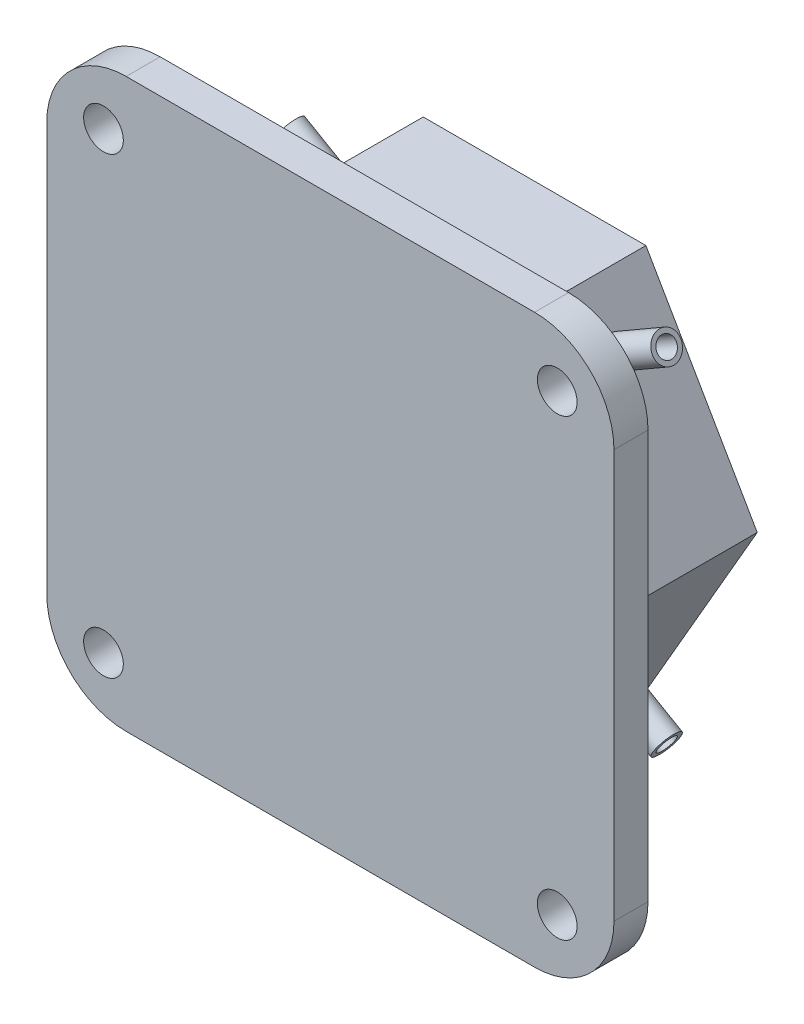
SolidWorks part; units mm, degrees
ref_plane "前视基准面" through (0, 0, 0) normal (0, 0, 1) x (1, 0, 0)
ref_plane "上视基准面" through (0, 0, 0) normal (0, 1, 0) x (1, 0, 0)
ref_plane "右视基准面" through (0, 0, 0) normal (1, 0, 0) x (0, 0, -1)
other "Configuration Table"
sketch "草图1" plane through (0, 0, 0) normal (0, 0, 1) x (1, 0, 0)
  line L1 (-18, -25) -> (18, -25)
  line L2 (-25, -18) -> (-25, 18)
  line L3 (-18, 25) -> (18, 25)
  line L4 (25, -18) -> (25, 18)
  line L5 (-25, -25) -> (25, 25) construction
  line L6 (-25, 25) -> (25, -25) construction
  circle A0 centre (20, 20) radius 1.75
  circle A1 centre (-20, 20) radius 1.75
  circle A2 centre (-20, -20) radius 1.75
  circle A3 centre (20, -20) radius 1.75
  arc A4 (18, -25) -> (25, -18) centre (18, -18) ccw
  arc A5 (-18, -25) -> (-25, -18) centre (-18, -18) cw
  arc A6 (18, 25) -> (25, 18) centre (18, 18) cw
  arc A7 (-25, 18) -> (-18, 25) centre (-18, 18) cw
  point P0 (0, 0)
  point P6 (20, 20)
  dimension "D3" = 5
  dimension "D6" = 3.5
  dimension "D7" = 3.5
  dimension "D4" = 3.5
  dimension "D8" = 3.5
  dimension "D11" = 7
  dimension "D1" = 50
  dimension "D2" = 50
  dimension "D5" = 5
  dimension "D9" = 5
  dimension "D10" = 5
extrude "凸台-拉伸3" add sketch "草图1" along normal blind 3 contours L2 A7 L3 A6 L4 A4 L1 A5 | A1 | A0 | A3 | A2
sketch "草图2" plane through (0, 0, 0) normal (0, 0, -1) x (-1, 0, 0)
  line L0 (18, 25) -> (-18, 25) construction
  line L1 (9.815, -17) -> (19.6299, 0)
  line L2 (19.6299, 0) -> (9.815, 17)
  line L3 (9.815, 17) -> (-9.815, 17)
  line L4 (-9.815, 17) -> (-19.6299, 0)
  line L5 (-19.6299, 0) -> (-9.815, -17)
  line L6 (-9.815, -17) -> (9.815, -17)
  circle A0 centre (0, 0) radius 17 construction
  dimension "D1" = 8
extrude "凸台-拉伸4" add sketch "草图2" along normal blind 15 contours L1 L2 L3 L4 L5 L6
sketch "草图3" plane through (0, 0, -15) normal (0, 0, -1) x (-1, 0, 0)
  line L2 (9.815, 17) -> (-9.815, 17) construction
  line L3 (0, 0) -> (-4.8151, 8.34) construction
  line L6 (-9.815, 17) -> (-19.6299, 0) construction
  line L7 (0, 0) -> (4.8151, 8.34) construction
  line L9 (19.6299, 0) -> (9.815, 17) construction
  circle A0 centre (-4.8151, 8.34) radius 1
  circle A6 centre (4.8151, 8.34) radius 1
  circle A8 centre (4.8151, -8.34) radius 1
  circle A9 centre (-4.8151, -8.34) radius 1
  circle A11 centre (-9.6302, 0) radius 1 [skipped]
  circle A12 centre (9.6302, 0) radius 1 [skipped]
  dimension "D3" = 2
  dimension "D6" = 2
  dimension "D7" = 8.66
  dimension "D2" = 8.66
  dimension "D4" = 6
  dimension "D1" = 8.66
  dimension "D5" = 60
  dimension "D8" = 8.66
extrude "切除-拉伸5" cut sketch "草图3" against normal blind 7.5
sketch "草图8" plane through (14.7224, 8.5, 0) normal (0.866, 0.5, 0) x (0, 0, -1)
  line L0 (15, 9.815) -> (15, -9.815) construction
  line L2 (15, 9.815) -> (0, 9.815) construction
  circle A0 centre (10, 4.815) radius 0.85
  point P6 (0, 0)
  point P7 (0, 0)
  dimension "D1" = 5
  dimension "D3" = 1.7
  dimension "D2" = 5
extrude "切除-拉伸8" cut sketch "草图8" against normal blind 9
sketch "草图10" plane through (-14.7224, 8.5, 0) normal (-0.866, 0.5, 0) x (0, 0, 1)
  line L0 (-15, 9.815) -> (0, 9.815) construction
  line L1 (-15, -9.815) -> (-15, 9.815) construction
  circle A0 centre (-10, 4.815) radius 0.85
  dimension "D1" = 5
  dimension "D3" = 1.7
  dimension "D2" = 5
extrude "切除-拉伸9" cut sketch "草图10" against normal blind 9
sketch "草图11" plane through (-14.7224, -8.5, 0) normal (-0.866, -0.5, 0) x (0, 0, 1)
  line L0 (-15, -9.815) -> (-15, 9.815) construction
  line L1 (-15, -9.815) -> (0, -9.815) construction
  circle A0 centre (-10, -4.815) radius 0.85
  dimension "D1" = 5
  dimension "D3" = 1.7
  dimension "D2" = 5
extrude "切除-拉伸10" cut sketch "草图11" against normal blind 9
sketch "草图12" plane through (14.7224, -8.5, 0) normal (0.866, -0.5, 0) x (0, 0, -1)
  line L0 (15, 9.815) -> (15, -9.815) construction
  line L1 (15, -9.815) -> (0, -9.815) construction
  circle A0 centre (10, -4.815) radius 0.85
  dimension "D1" = 5
  dimension "D3" = 1.7
  dimension "D2" = 5
extrude "切除-拉伸11" cut sketch "草图12" against normal blind 9
sketch "草图13" plane through (14.7224, 8.5, 0) normal (0.866, 0.5, 0) x (0, 0, -1)
  circle A0 centre (10, 4.815) radius 1.25
  circle A1 centre (10, 4.815) radius 0.85
  dimension "D1" = 2.5
  dimension "D2" = 1.7
extrude "凸台-拉伸5" add sketch "草图13" along normal blind 5
sketch "草图14" plane through (-14.7224, 8.5, 0) normal (-0.866, 0.5, 0) x (0, 0, 1)
  circle A0 centre (-10, 4.815) radius 1.25
  circle A1 centre (-10, 4.815) radius 0.85
  dimension "D1" = 2.5
  dimension "D2" = 1.7
extrude "凸台-拉伸6" add sketch "草图14" along normal blind 5
sketch "草图15" plane through (-14.7224, -8.5, 0) normal (-0.866, -0.5, 0) x (0, 0, 1)
  circle A0 centre (-10, -4.815) radius 1.25
  circle A1 centre (-10, -4.815) radius 0.85
  dimension "D1" = 2.5
  dimension "D2" = 1.7
extrude "凸台-拉伸7" add sketch "草图15" along normal blind 5
sketch "草图16" plane through (14.7224, -8.5, 0) normal (0.866, -0.5, 0) x (0, 0, -1)
  circle A0 centre (10, -4.815) radius 1.25
  circle A1 centre (10, -4.815) radius 0.85
  dimension "D1" = 2.5
  dimension "D2" = 1.7
extrude "凸台-拉伸8" add sketch "草图16" along normal blind 5
sketch "草图17" plane through (0, 0, -15) normal (0, 0, -1) x (-1, 0, 0)
  circle A0 centre (4.8151, 8.34) radius 1.25
  circle A1 centre (4.8151, 8.34) radius 1
  circle A2 centre (-4.8151, 8.34) radius 1
  circle A3 centre (-4.8151, 8.34) radius 1.25
  circle A4 centre (-4.8151, -8.34) radius 1
  circle A5 centre (-4.8151, -8.34) radius 1.25
  circle A6 centre (4.8151, -8.34) radius 1
  circle A7 centre (4.8151, -8.34) radius 1.25
  dimension "D1" = 2.5
  dimension "D2" = 2
  dimension "D3" = 2.5
  dimension "D4" = 2
  dimension "D5" = 2.5
  dimension "D6" = 2
  dimension "D7" = 2.5
  dimension "D8" = 2
extrude "凸台-拉伸9" add sketch "草图17" along normal blind 5
